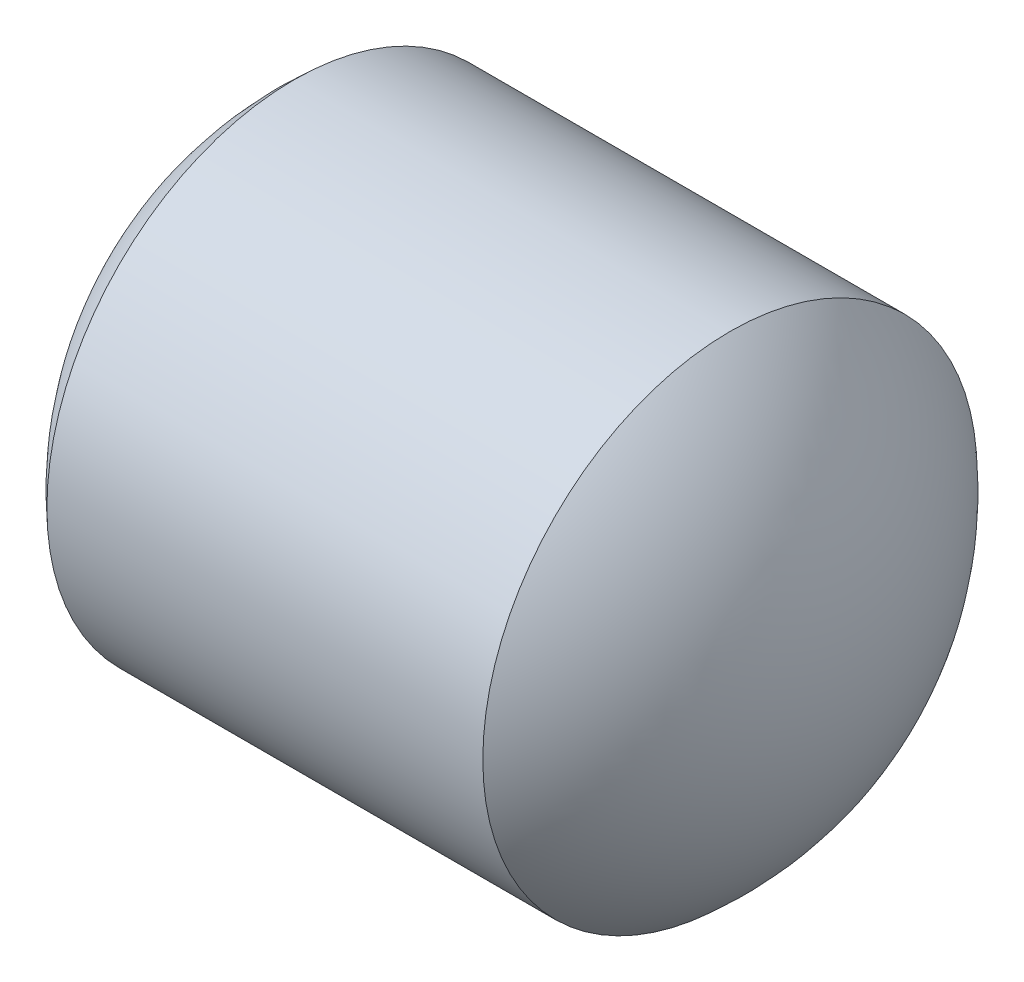
SolidWorks part; units mm, degrees
ref_plane "前视基准面" through (0, 0, 0) normal (0, 0, 1) x (1, 0, 0)
ref_plane "上视基准面" through (0, 0, 0) normal (0, 1, 0) x (1, 0, 0)
ref_plane "右视基准面" through (0, 0, 0) normal (1, 0, 0) x (0, 0, -1)
sketch "草图1" plane through (0, 0, 0) normal (0, 0, 1) x (1, 0, 0)
  line L0 (227.5435, 133.3449) -> (231.8061, 133.3449) construction
  line L1 (229.6993, 134.8449) -> (228.3765, 134.8449)
  line L2 (228.3765, 134.8449) -> (228.3765, 133.3449)
  line L3 (229.6993, 134.8449) -> (231.0222, 134.8449)
  line L4 (231.0222, 134.8449) -> (231.0222, 133.3449)
  line L5 (229.6993, 131.8449) -> (228.3765, 131.8449)
  line L6 (228.3765, 131.8449) -> (228.3765, 133.3449)
  line L7 (229.6993, 131.8449) -> (231.0222, 131.8449)
  line L8 (231.0222, 131.8449) -> (231.0222, 133.3449)
  arc A0 (228.3765, 134.8449) -> (228.3765, 131.8449) centre (229.6993, 133.3449) ccw
  arc A1 (231.0222, 131.8449) -> (231.0222, 134.8449) centre (229.6993, 133.3449) ccw
  dimension "D1" = 2
  dimension "D2" = 3
revolve "旋转1" add sketch "草图1" angle 360 about L0
